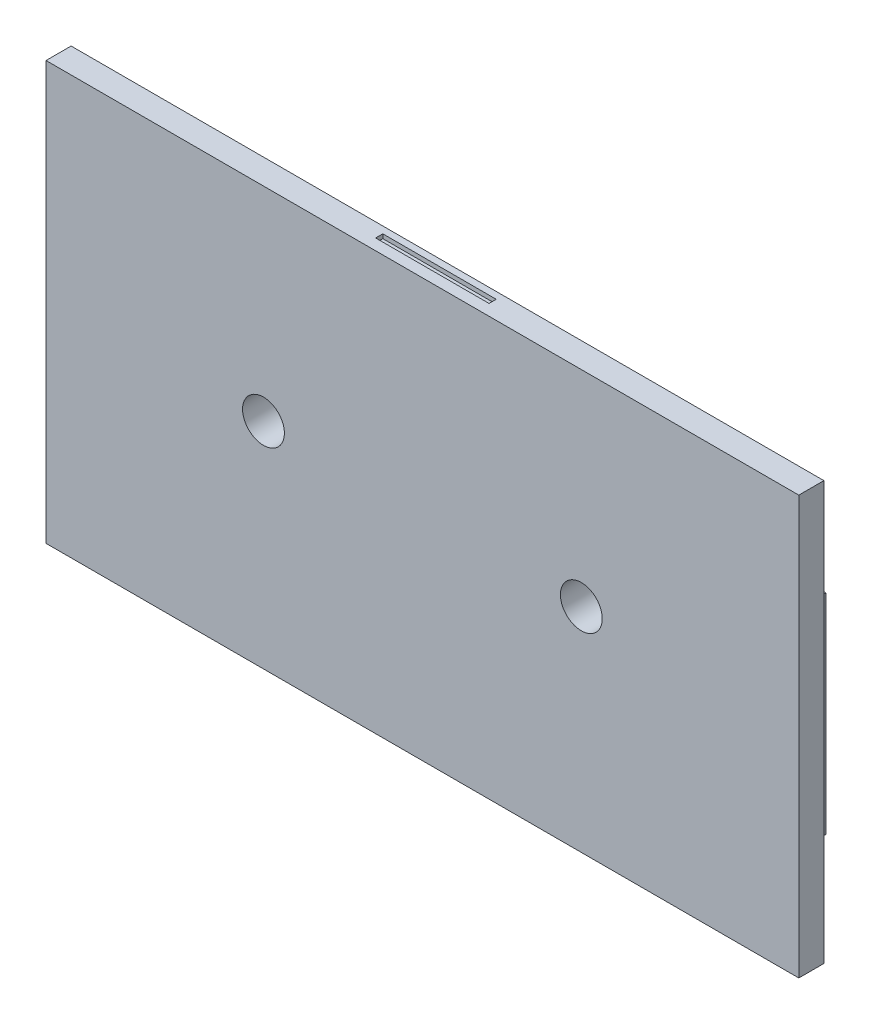
SolidWorks part; units mm, degrees
ref_plane "Piano frontale" through (0, 0, 0) normal (0, 0, 1) x (1, 0, 0)
ref_plane "Piano superiore" through (0, 0, 0) normal (0, 1, 0) x (1, 0, 0)
ref_plane "Piano destro" through (0, 0, 0) normal (1, 0, 0) x (0, 0, -1)
sketch "Schizzo1" plane through (0, 0, 0) normal (0, 0, 1) x (1, 0, 0)
  line L0 (-90, -50) -> (-90, 50)
  line L1 (-90, 50) -> (90, 50)
  line L2 (90, 50) -> (90, -50)
  line L3 (90, -50) -> (-90, -50)
  line L4 (-85, 45) -> (-85, -45)
  line L5 (-85, -45) -> (85, -45)
  line L6 (85, -45) -> (85, 45)
  line L7 (85, 45) -> (-85, 45)
  dimension "D1" = 90
  dimension "D2" = 170
  dimension "D3" = 5
  dimension "D4" = 5
  dimension "D5" = 5
  dimension "D6" = 5
extrude "Estrusione-Estrusione1" add sketch "Schizzo1" along normal blind 6
sketch "Schizzo2" plane through (-85, 0, 0) normal (1, 0, 0) x (0, 0, -1)
  line L0 (-6, -50) -> (0, -50) construction
  line L1 (-6, 50) -> (-5.15, 50)
  line L2 (-6, 50) -> (-6, -50)
  line L3 (-6, -50) -> (-5.15, -50)
  line L4 (-5.15, 50) -> (-5.15, -50)
  dimension "D1" = 0.85
extrude "Estrusione-Estrusione2" add sketch "Schizzo2" along normal up to surface (170 mm away) up to face at (85, 0, 3)
sketch "Schizzo3" plane through (0, 0, 5.15) normal (0, 0, -1) x (-1, 0, 0)
  line L0 (85, -45) -> (-85, -45) construction
  line L1 (-85, -45) -> (-85, 45) construction
  circle A0 centre (-38, 0.9) radius 9.25
  circle A1 centre (-38, 0.9) radius 12.5
  circle A2 centre (38, 1.3) radius 9.25
  circle A3 centre (38, 1.3) radius 12.5
  dimension "D1" = 18.5
  dimension "D2" = 25
  dimension "D5" = 25
  dimension "D7" = 18.5
  dimension "D8" = 0.4
  dimension "D3" = 45.9
  dimension "D4" = 47
  dimension "D6" = 76
extrude "Estrusione-Estrusione3" add sketch "Schizzo3" along normal blind 10
sketch "Schizzo4" plane through (0, 0, 5.15) normal (0, 0, -1) x (-1, 0, 0)
  circle A0 centre (-38, 0.9) radius 5
  circle A1 centre (38, 1.3) radius 5
  circle A4 centre (-38, 0.9) radius 9.25 construction
  circle A5 centre (38, 1.3) radius 9.25 construction
  dimension "D1" = 10
extrude "Taglio-Estrusione1" cut sketch "Schizzo4" against normal blind 30
sketch "Schizzo5" plane through (0, 0, 0) normal (0, 0, -1) x (-1, 0, 0)
  line L4 (-88.5, 25) -> (-86.5, 25)
  line L5 (-88.5, 25) -> (-88.5, -25)
  line L6 (-88.5, -25) -> (-86.5, -25)
  line L7 (-86.5, 25) -> (-86.5, -25)
  line L8 (-90, -50) -> (-90, 50) construction
  dimension "D2" = 2
  dimension "D3" = 20
  dimension "D4" = 1.5
  dimension "D5" = 20
extrude "Estrusione-Estrusione4" add sketch "Schizzo5" along normal blind 2
ref_plane "Piano1" through (0, 0, 0) normal (-1, 0, 0) x (0, 0, 1)
mirror "Specchia1" about plane through (0, 0, 0) normal (-1, 0, 0) of "Estrusione-Estrusione4"
sketch "Schizzo10" plane through (0, 0, 5.15) normal (0, 0, -1) x (-1, 0, 0)
  circle A0 centre (-38, 0.9) radius 9.25
  circle A1 centre (-38, 0.9) radius 5
  circle A2 centre (-38, 0.9) radius 5 construction
  circle A3 centre (-38, 0.9) radius 9.25 construction
extrude "Estrusione-Estrusione7" add sketch "Schizzo10" along normal blind 8.5
sketch "Schizzo11" plane through (0, 0, 5.15) normal (0, 0, -1) x (-1, 0, 0)
  circle A0 centre (38, 1.3) radius 5
  circle A1 centre (38, 1.3) radius 9.25
  circle A2 centre (38, 1.3) radius 5 construction
  circle A3 centre (38, 1.3) radius 9.25 construction
extrude "Estrusione-Estrusione8" add sketch "Schizzo11" along normal blind 8.5
sketch "Schizzo12" plane through (0, 50, 0) normal (0, 1, 0) x (1, 0, 0)
  line L0 (-13.842, -1.6251) -> (13.2692, -1.6251)
  line L1 (13.2692, -1.6251) -> (13.2692, -3.3434)
  line L2 (13.2692, -3.3434) -> (-13.842, -3.3434)
  line L3 (-13.842, -3.3434) -> (-13.842, -1.6251)
  point P2 (-12.5055, 0.2842)
extrude "Taglio-Estrusione2" cut sketch "Schizzo12" against normal blind 1
